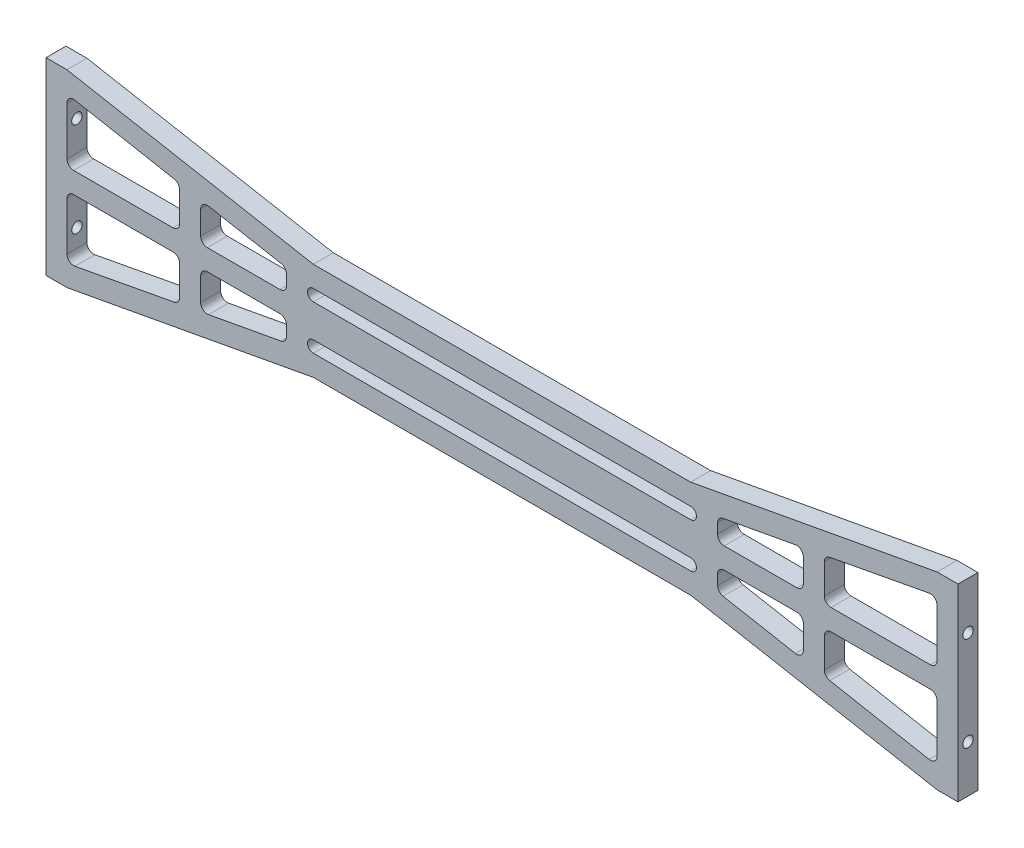
SolidWorks part; units mm, degrees
material "6061-T6 (SS)"
ref_plane "Front Plane" through (0, 0, 0) normal (0, 0, 1) x (1, 0, 0)
ref_plane "Top Plane" through (0, 0, 0) normal (0, 1, 0) x (1, 0, 0)
ref_plane "Right Plane" through (0, 0, 0) normal (1, 0, 0) x (0, 0, -1)
sketch "Sketch3" plane through (0, 0, 0) normal (0, 0, 1) x (1, 0, 0)
  line L0 (-108.763, -0.017) -> (108.763, 0.017) construction
  line L1 (-45, -5.3033) -> (45, -5.3033) construction
  line L2 (0, 0) -> (0, 81.4109) construction
  line L3 (0, 0) -> (0, -81.4109) construction
  line L4 (-108.763, 22.483) -> (-108.763, -22.517)
  line L5 (-108.763, 22.483) -> (-103.763, 22.483)
  line L6 (108.763, -22.483) -> (108.763, 22.517)
  line L7 (-45, -3.9234) -> (45, -3.9234)
  line L8 (-45, 5.3033) -> (45, 5.3033) construction
  line L9 (-45, 6.6832) -> (45, 6.6832)
  line L10 (-45, 3.9234) -> (45, 3.9234)
  line L11 (-45, -6.6832) -> (45, -6.6832)
  line L12 (-103.763, 22.483) -> (-45, 11.6832)
  line L13 (-45, 11.6832) -> (45, 11.6832)
  line L14 (45, 11.6832) -> (103.763, 22.517)
  line L15 (103.763, -22.483) -> (45, -11.6832)
  line L16 (103.763, 22.517) -> (108.763, 22.517)
  line L17 (108.763, -22.483) -> (103.763, -22.483)
  line L18 (45, -11.6832) -> (-45, -11.6832)
  line L19 (-45, -11.6832) -> (-103.763, -22.517)
  line L20 (-103.763, 15.5713) -> (-103.763, 4.0713)
  line L21 (-52.7219, -8.0355) -> (-70.0035, -11.2172)
  line L22 (-101.8838, 17.1318) -> (-78.1773, 12.701)
  line L23 (-103.763, -22.517) -> (-108.763, -22.517)
  line L24 (-76.8815, 11.1405) -> (-76.8815, 4.0713)
  line L25 (-78.469, 2.4838) -> (-102.1755, 2.4838)
  line L26 (-103.763, 22.483) -> (-103.763, -22.517) construction
  line L27 (-71.8815, 9.634) -> (-71.8815, 4.0713)
  line L28 (103.763, -22.483) -> (103.763, 22.517) construction
  line L29 (-70.294, 2.4838) -> (-52.985, 2.4838)
  line L30 (-51.3976, 4.0888) -> (-51.424, 6.4753)
  line L31 (-52.7244, 8.0191) -> (-70.007, 11.1954)
  line L32 (-51.3963, -4.1049) -> (-51.422, -6.4913)
  line L33 (-70.2932, -2.5057) -> (-52.9842, -2.5003)
  line L34 (-71.8785, -9.6565) -> (-71.8802, -4.0937)
  line L35 (-78.4682, -2.5083) -> (-102.1747, -2.5157)
  line L36 (-76.878, -11.1645) -> (-76.8802, -4.0953)
  line L37 (-101.8785, -17.1636) -> (-78.1734, -12.7254)
  line L38 (-103.7581, -15.6037) -> (-103.7617, -4.1037)
  line L39 (103.7581, -15.6037) -> (103.7617, -4.1037)
  line L40 (101.8785, -17.1636) -> (78.1734, -12.7254)
  line L41 (76.878, -11.1645) -> (76.8802, -4.0953)
  line L42 (78.4682, -2.5083) -> (102.1747, -2.5157)
  line L43 (71.8785, -9.6565) -> (71.8802, -4.0937)
  line L44 (70.2932, -2.5057) -> (52.9842, -2.5003)
  line L45 (51.3963, -4.1049) -> (51.422, -6.4913)
  line L46 (52.7219, -8.0355) -> (70.0035, -11.2172)
  line L47 (52.7194, 8.052) -> (70, 11.2391)
  line L48 (51.395, 4.1209) -> (51.4199, 6.5074)
  line L49 (70.2924, 2.5277) -> (52.9834, 2.5169)
  line L50 (71.8755, 9.6789) -> (71.8789, 4.1162)
  line L51 (78.4674, 2.5328) -> (102.1739, 2.5476)
  line L52 (76.8745, 11.1885) -> (76.8789, 4.1193)
  line L53 (101.8731, 17.1954) -> (78.1694, 12.7498)
  line L54 (103.7533, 15.6361) -> (103.7604, 4.1361)
  arc A0 (-45, 6.6832) -> (-45, 3.9234) centre (-45, 5.3033) ccw
  arc A1 (45, 3.9234) -> (45, 6.6832) centre (45, 5.3033) ccw
  arc A2 (-45, -3.9234) -> (-45, -6.6832) centre (-45, -5.3033) ccw
  arc A3 (45, -6.6832) -> (45, -3.9234) centre (45, -5.3033) ccw
  arc A4 (-52.985, 2.4838) -> (-51.3976, 4.0888) centre (-52.985, 4.0713) ccw
  arc A5 (-51.424, 6.4753) -> (-52.7244, 8.0191) centre (-53.0114, 6.4577) ccw
  arc A6 (-71.8815, 4.0713) -> (-70.294, 2.4838) centre (-70.294, 4.0713) ccw
  arc A7 (-71.8815, 9.634) -> (-70.007, 11.1954) centre (-70.294, 9.634) cw
  arc A8 (-76.8815, 4.0713) -> (-78.469, 2.4838) centre (-78.469, 4.0713) cw
  arc A9 (-76.8815, 11.1405) -> (-78.1773, 12.701) centre (-78.469, 11.1405) ccw
  arc A10 (-103.763, 4.0713) -> (-102.1755, 2.4838) centre (-102.1755, 4.0713) ccw
  arc A11 (-103.763, 15.5713) -> (-101.8838, 17.1318) centre (-102.1755, 15.5713) cw
  arc A12 (-103.7581, -15.6037) -> (-101.8785, -17.1636) centre (-102.1706, -15.6032) ccw
  arc A13 (-103.7617, -4.1037) -> (-102.1747, -2.5157) centre (-102.1742, -4.1032) cw
  arc A14 (-76.878, -11.1645) -> (-78.1734, -12.7254) centre (-78.4655, -11.165) cw
  arc A15 (-76.8802, -4.0953) -> (-78.4682, -2.5083) centre (-78.4677, -4.0958) ccw
  arc A16 (-71.8785, -9.6565) -> (-70.0035, -11.2172) centre (-70.291, -9.656) ccw
  arc A17 (-71.8802, -4.0937) -> (-70.2932, -2.5057) centre (-70.2927, -4.0932) cw
  arc A18 (-51.422, -6.4913) -> (-52.7219, -8.0355) centre (-53.0094, -6.4743) cw
  arc A19 (-52.9842, -2.5003) -> (-51.3963, -4.1049) centre (-52.9837, -4.0878) cw
  arc A20 (52.9842, -2.5003) -> (51.3963, -4.1049) centre (52.9837, -4.0878) ccw
  arc A21 (51.422, -6.4913) -> (52.7219, -8.0355) centre (53.0094, -6.4743) ccw
  arc A22 (71.8802, -4.0937) -> (70.2932, -2.5057) centre (70.2927, -4.0932) ccw
  arc A23 (71.8785, -9.6565) -> (70.0035, -11.2172) centre (70.291, -9.656) cw
  arc A24 (76.8802, -4.0953) -> (78.4682, -2.5083) centre (78.4677, -4.0958) cw
  arc A25 (76.878, -11.1645) -> (78.1734, -12.7254) centre (78.4655, -11.165) ccw
  arc A26 (103.7617, -4.1037) -> (102.1747, -2.5157) centre (102.1742, -4.1032) ccw
  arc A27 (103.7581, -15.6037) -> (101.8785, -17.1636) centre (102.1706, -15.6032) cw
  arc A28 (103.7533, 15.6361) -> (101.8731, 17.1954) centre (102.1658, 15.6351) ccw
  arc A29 (103.7604, 4.1361) -> (102.1739, 2.5476) centre (102.1729, 4.1351) cw
  arc A30 (76.8745, 11.1885) -> (78.1694, 12.7498) centre (78.462, 11.1895) cw
  arc A31 (76.8789, 4.1193) -> (78.4674, 2.5328) centre (78.4664, 4.1203) ccw
  arc A32 (71.8755, 9.6789) -> (70, 11.2391) centre (70.288, 9.6779) ccw
  arc A33 (71.8789, 4.1162) -> (70.2924, 2.5277) centre (70.2914, 4.1152) cw
  arc A34 (51.4199, 6.5074) -> (52.7194, 8.052) centre (53.0073, 6.4908) cw
  arc A35 (52.9834, 2.5169) -> (51.395, 4.1209) centre (52.9825, 4.1044) cw
  point P11 (-108.763, -0.017)
  point P14 (0, -5.3033)
  point P19 (0, 5.3033)
  point P20 (103.763, 22.517)
  point P21 (45, -5.3033)
  point P22 (-103.763, 22.483)
  point P23 (-103.763, -22.517)
  point P24 (-45, -5.3033)
  point P27 (-45, 11.6832)
  point P28 (103.763, -22.483)
  point P30 (45, 11.6832)
  point P31 (-45, -11.6832)
  point P32 (45, -11.6832)
  point P40 (-103.763, 17.483)
  point P46 (103.763, -17.517)
  point P50 (103.763, 17.483)
  point P52 (-45, 5.3033)
  point P53 (45, 5.3033)
  point P57 (-103.763, 2.4838)
  point P59 (103.763, 2.4838)
  point P60 (103.763, -2.5162)
  point P62 (-5.3033, 5.3033)
  point P63 (5.3033, 5.3033)
  point P64 (5.3033, -5.3033)
  point P65 (-5.3033, -5.3033)
  point P67 (-74.3815, 17.0831)
  point P68 (-74.3815, 5.3033)
  point P71 (-76.8815, 5.3033)
  point P72 (-71.8815, 5.3033)
  point P75 (-76.8815, 2.4838)
  point P76 (-51.3799, 2.4838)
  point P78 (-71.8815, 2.4838)
  point P81 (-71.8815, 11.5399)
  point P82 (-51.3799, 5.3033)
  point P83 (-46.3799, 5.3033)
  point P84 (-51.3799, 2.4838)
  point P92 (-71.8815, 2.4838)
  point P95 (-71.8815, 11.5399)
  point P98 (-76.8815, 2.4838)
  point P103 (-103.763, 2.4838)
  point P106 (-103.763, 17.483)
  point P119 (-103.7575, -17.5154)
  point P120 (-103.7622, -2.5162)
  point P121 (-76.8807, -2.5078)
  point P122 (-71.8779, -11.5623)
  point P123 (-71.8807, -2.5062)
  point P124 (-51.3791, -2.4998)
  point P125 (-51.3782, -5.3193)
  point P126 (-71.8798, -5.3257)
  point P127 (-76.8798, -5.3273)
  point P128 (-74.3798, -5.3265)
  point P129 (-74.3762, -17.1063)
  point P154 (74.3762, -17.1063)
  point P155 (74.3798, -5.3265)
  point P156 (76.8798, -5.3273)
  point P157 (71.8798, -5.3257)
  point P158 (51.3782, -5.3193)
  point P159 (51.3791, -2.4998)
  point P160 (71.8807, -2.5062)
  point P161 (71.8779, -11.5623)
  point P162 (76.8807, -2.5078)
  point P163 (103.7622, -2.5162)
  point P164 (103.7575, -17.5154)
  point P189 (103.7521, 17.5478)
  point P190 (103.7614, 2.5486)
  point P191 (76.8799, 2.5318)
  point P192 (71.8743, 11.5848)
  point P193 (71.8799, 2.5287)
  point P194 (51.3783, 2.5159)
  point P195 (51.3765, 5.3354)
  point P196 (71.8782, 5.3482)
  point P197 (76.8782, 5.3513)
  point P198 (74.3782, 5.3498)
  point P199 (74.3708, 17.1295)
  point P200 (103.7622, 2.5486)
  point P201 (103.7575, 17.5494)
  dimension "D1" = 5
  dimension "D2" = 45
  dimension "D3" = 217.526
  dimension "D4" = 5
  dimension "D5" = 5
  dimension "D7" = 1.5875
  dimension "D6" = 5
  dimension "D9" = 5
  dimension "D17" = 2.5
  dimension "D19" = 2.5
  dimension "D20" = 5
  dimension "D23" = 5
extrude "Boss-Extrude1" add sketch "Sketch3" along normal blind 4.763
hole_wizard "Tap Drill for M3x0.5 Tap1" positions "Sketch8" profile "Sketch7" hole size "M3x0.5" standard "ANSI Metric"
sketch "Sketch8" plane through (108.763, 0, 0) normal (1, 0, 0) x (0, 0, -1)
  line L3 (-2.3815, 22.517) -> (-2.3815, -22.483) construction
  line L4 (-4.763, 22.517) -> (0, 22.517) construction
  line L5 (-4.763, -22.483) -> (0, -22.483) construction
  point P0 (-2.3815, 11.267)
  point P2 (-2.3815, -11.233)
  dimension "D1" = 11.25
  dimension "D2" = 11.25
sketch "Sketch7" plane through (108.763, 11.267, 2.3815) normal (0, 1, 0) x (0, 0, -1)
  line L0 (0, 0) -> (0, 5.007)
  line L1 (0, 5.007) -> (1.25, 5.007)
  line L2 (1.25, 5.007) -> (1.25, 0)
  line L5 (1.25, 0) -> (0, 0)
  line L11 (0, -6.35) -> (0, 107.95) construction
  dimension "Thru Hole Dia." = 2.5
  dimension "Thru Hole Depth" = 5.007
hole_wizard "Tap Drill for M3x0.5 Tap2" positions "Sketch10" profile "Sketch9" hole size "M3x0.5" standard "ANSI Metric"
sketch "Sketch10" plane through (-108.763, 0, 0) normal (-1, 0, 0) x (0, 0, 1)
  line L3 (2.3815, 22.483) -> (2.3815, -22.517) construction
  line L4 (4.763, 22.483) -> (0, 22.483) construction
  line L5 (4.763, -22.517) -> (0, -22.517) construction
  point P0 (2.3815, 11.233)
  point P2 (2.3815, -11.267)
  dimension "D1" = 11.25
  dimension "D2" = 11.25
sketch "Sketch9" plane through (-108.763, 11.233, 2.3815) normal (0, 1, 0) x (0, 0, 1)
  line L0 (0, 0) -> (0, 5)
  line L1 (0, 5) -> (1.25, 5)
  line L2 (1.25, 5) -> (1.25, 0)
  line L5 (1.25, 0) -> (0, 0)
  line L11 (0, -6.35) -> (0, 107.95) construction
  dimension "Thru Hole Dia." = 2.5
  dimension "Thru Hole Depth" = 5
